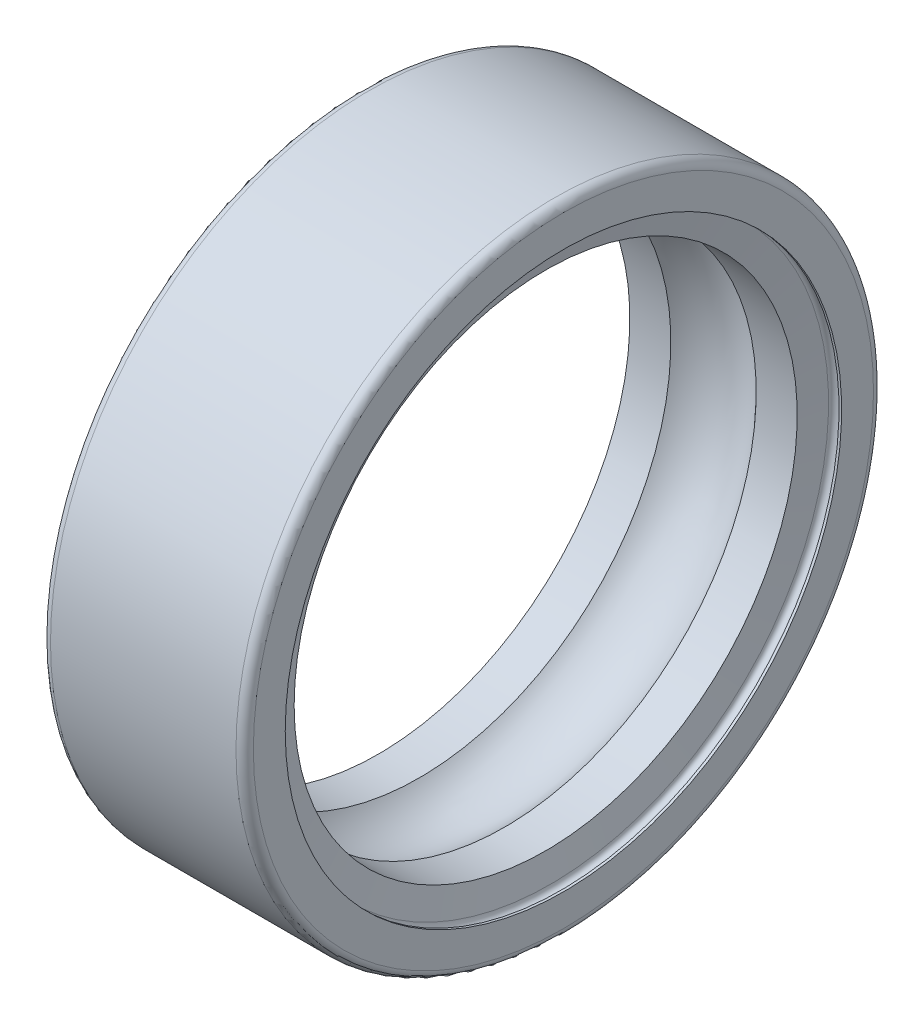
SolidWorks part; units mm, degrees
ref_plane "Ebene vorne" through (0, 0, 0) normal (0, 0, 1) x (1, 0, 0)
ref_plane "Ebene oben" through (0, 0, 0) normal (0, 1, 0) x (1, 0, 0)
ref_plane "Ebene rechts" through (0, 0, 0) normal (1, 0, 0) x (0, 0, -1)
ref_plane "Ebene1" through (0, 0, 0) normal (0, 0, 1) x (1, 0, 0)
sketch "Skizze1" plane through (0, 0, 0) normal (0, 0, 1) x (1, 0, 0)
  line L0 (0, 9.6) -> (0.09, 9.6)
  line L1 (0.45, 9.6) -> (0.6122, 8.68)
  line L2 (0.6122, 8.68) -> (2.0271, 8.68)
  line L3 (4.9729, 8.68) -> (6.3878, 8.68)
  line L4 (6.3878, 8.68) -> (6.55, 9.6)
  line L5 (6.91, 9.6) -> (7, 9.6)
  line L6 (7, 9.6) -> (7, 10.7)
  line L7 (6.7, 11) -> (0.3, 11)
  line L8 (0, 10.7) -> (0, 9.6)
  line L9 (50, 0) -> (-50, 0) construction
  arc A0 (0.09, 9.6) -> (0.45, 9.6) centre (0.27, 9.6) cw
  arc A1 (2.0271, 8.68) -> (4.9729, 8.68) centre (3.5, 7.35) cw
  arc A2 (6.55, 9.6) -> (6.91, 9.6) centre (6.73, 9.6) cw
  arc A3 (7, 10.7) -> (6.7, 11) centre (6.7, 10.7) ccw
  arc A4 (0.3, 11) -> (0, 10.7) centre (0.3, 10.7) ccw
revolve "Rotation1" add sketch "Skizze1" angle 360 about L9
